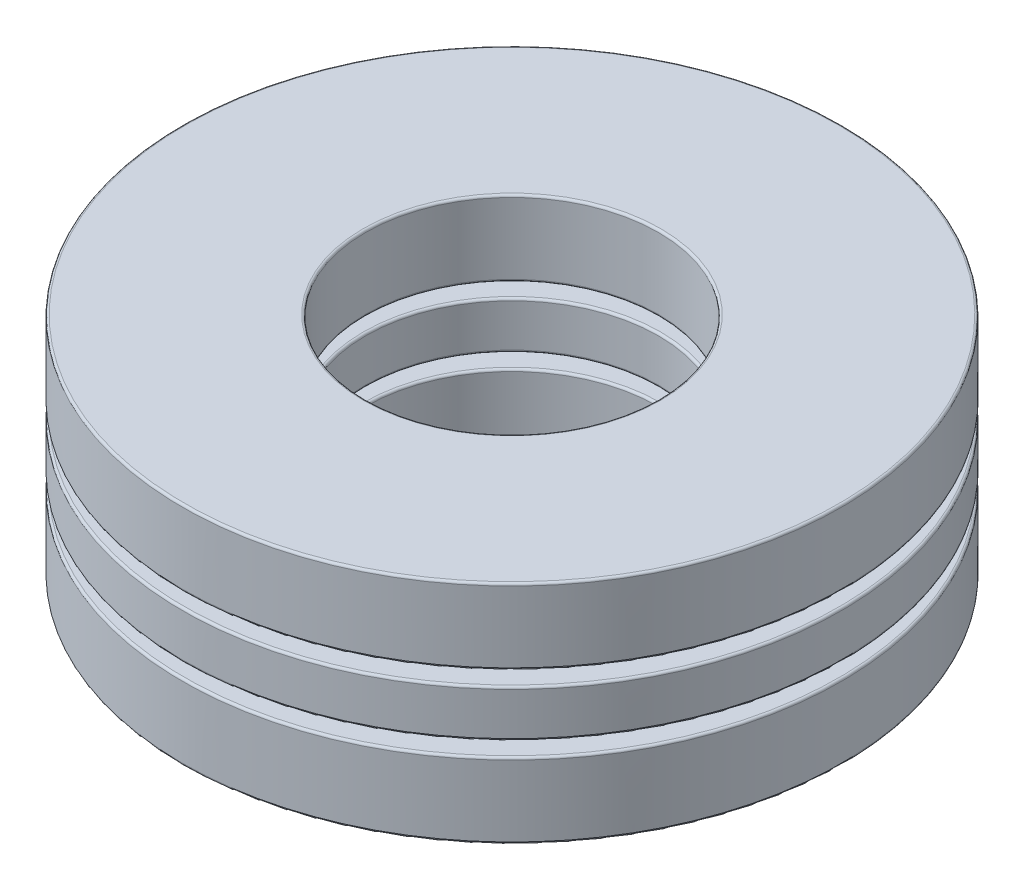
SolidWorks part; units mm, degrees
ref_plane "Front Plane" through (0, 0, 0) normal (0, 0, 1) x (1, 0, 0)
ref_plane "Top Plane" through (0, 0, 0) normal (0, 1, 0) x (1, 0, 0)
ref_plane "Right Plane" through (0, 0, 0) normal (1, 0, 0) x (0, 0, -1)
sketch "Sketch1" plane through (0, 0, 0) normal (1, 0, 0) x (0, 0, -1)
  line L0 (-7.1438, 0) -> (7.1438, 0) construction
  line L1 (0, -2.4511) -> (0, 2.4511) construction
  line L2 (-7.1438, 0.5106) -> (-3.175, 0.5106)
  line L3 (-7.1438, 0.5106) -> (-7.1438, -0.5106)
  line L4 (-7.1438, -0.5106) -> (-3.175, -0.5106)
  line L5 (-3.175, 0.5106) -> (-3.175, -0.5106)
  line L6 (-5.1594, 0.817) -> (-5.1594, -0.817) construction
  circle A0 centre (-5.1594, 0) radius 0.817 construction
  point P13 (-5.1594, 0.5106)
  dimension "OD" = 14.2875
  dimension "Shaft Dia" = 6.35
  dimension "Th" = 4.9022
  dimension "D1" = 1.6341
  dimension "D2" = 1.0213
revolve "Revolve1" add sketch "Sketch1" angle 360 about L1
sketch "Sketch3" plane through (0, 0, 0) normal (1, 0, 0) x (0, 0, -1)
  line L0 (-5.1594, 0.817) -> (-5.1594, -0.817)
  arc A0 (-5.1594, 0.817) -> (-5.1594, -0.817) centre (-5.1594, 0) ccw
  circle A1 centre (-5.1594, 0) radius 0.817 construction
revolve "Cut-Revolve1" cut sketch "Sketch3" angle 360 about L0
sketch "Sketch2" plane through (0, 0, 0) normal (1, 0, 0) x (0, 0, -1)
  line L0 (-5.1594, 0.817) -> (-5.1594, -0.817)
  arc A0 (-5.1594, 0.817) -> (-5.1594, -0.817) centre (-5.1594, 0) ccw
  circle A2 centre (-5.1594, 0) radius 0.817 construction
revolve "Revolve2" add sketch "Sketch2" angle 360 about L0
ref_axis "Axis1" through (0, 2.4511, 0) along (0, -1, 0)
pattern_circular "CirPattern1" count 7 every 51.429 about axis through (0, 2.4511, 0) along (0, -1, 0) of bodies 187
pattern_circular "CirPattern2" count 7 every 51.429 about axis through (0, 0, 0) along (0, 1, 0) of "Cut-Revolve1"
sketch "Sketch4" plane through (0, 0, 0) normal (1, 0, 0) x (0, 0, -1)
  line L0 (-7.1438, 0.5106) -> (-7.1438, -0.5106) construction
  line L1 (-7.1438, 0.817) -> (-3.175, 0.817)
  line L2 (-7.1438, 0.817) -> (-7.1438, 2.4511)
  line L3 (-7.1438, 2.4511) -> (-3.175, 2.4511)
  line L4 (-3.175, 0.817) -> (-3.175, 2.4511)
  line L5 (-7.1438, -2.4511) -> (-3.175, -2.4511)
  line L6 (-7.1438, -2.4511) -> (-7.1438, -0.817)
  line L7 (-7.1438, -0.817) -> (-3.175, -0.817)
  line L8 (-3.175, -2.4511) -> (-3.175, -0.817)
  line L9 (-5.1594, 0.817) -> (-5.1594, -0.817) construction
  line L10 (-3.175, 0.5106) -> (-3.175, -0.5106) construction
  line L11 (0, 0) -> (-7.1438, 0) construction
  line L12 (-7.1438, 0) -> (7.1438, 0) construction
  dimension "Ht" = 4.9022
revolve "Revolve3" add sketch "Sketch4" angle 360 about L1
fillet "Fillet1" radius 0.049 4 edges at (0, 0.817, -3.175) (0, 2.4511, -3.175) (0, 0.817, -7.1438) (0, 2.4511, -7.1438)
fillet "Fillet2" radius 0.049 4 edges at (0, -0.5106, -3.175) (0, 0.5106, -3.175) (0, -0.5106, -7.1438) (0, 0.5106, -7.1438)
fillet "Fillet3" radius 0.049 4 edges at (0, -2.4511, -3.175) (0, -0.817, -3.175) (0, -2.4511, -7.1438) (0, -0.817, -7.1438)
equation "\"D1@Sketch1\" = \"Th@Sketch1\"/3"
equation "\"D2@Sketch1\" = \"D1@Sketch1\"*.625"
equation "\"Balls@CirPattern1\" = \"OD@Sketch1\"*12"
equation "\"Angle@CirPattern1\" = 360/\"Balls@CirPattern1\""
equation "\"D1@CirPattern2\" = \"Balls@CirPattern1\""
equation "\"D2@CirPattern2\" = \"Angle@CirPattern1\""
equation "\"D1@Fillet1\" = \"Th@Sketch1\"*.01"
equation "\"D1@Fillet2\" = \"D1@Fillet1\""
equation "\"D1@Fillet3\" = \"D1@Fillet1\""
